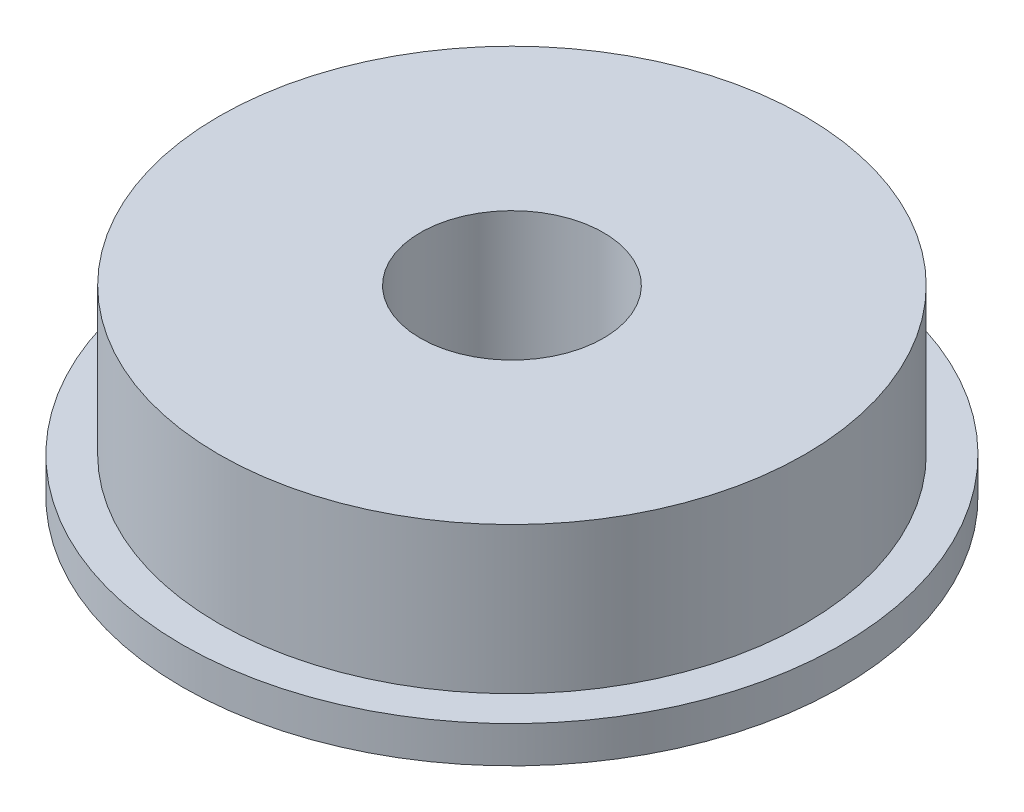
SolidWorks part; units mm, degrees
material "Stainless Steel (ferritic)"
ref_plane "Front Plane" through (0, 0, 0) normal (0, 0, 1) x (1, 0, 0)
ref_plane "Top Plane" through (0, 0, 0) normal (0, 1, 0) x (1, 0, 0)
ref_plane "Right Plane" through (0, 0, 0) normal (1, 0, 0) x (0, 0, -1)
sketch "Sketch1" plane through (0, 0, 0) normal (0, 1, 0) x (1, 0, 0)
  circle A0 centre (0, 0) radius 72
extrude "Boss-Extrude1" add sketch "Sketch1" along normal blind 8
sketch "Sketch2" plane through (0, 8, 0) normal (0, 1, 0) x (1, 0, 0)
  circle A0 centre (0, 0) radius 64
extrude "Boss-Extrude2" add sketch "Sketch2" along normal blind 32
sketch "Sketch3" plane through (0, 40, 0) normal (0, 1, 0) x (1, 0, 0)
  circle A0 centre (0, 0) radius 20
extrude "Cut-Extrude1" cut sketch "Sketch3" against normal through all
scale "Scale1" scale about centroid uniform scaling yes scale factor 0.125
